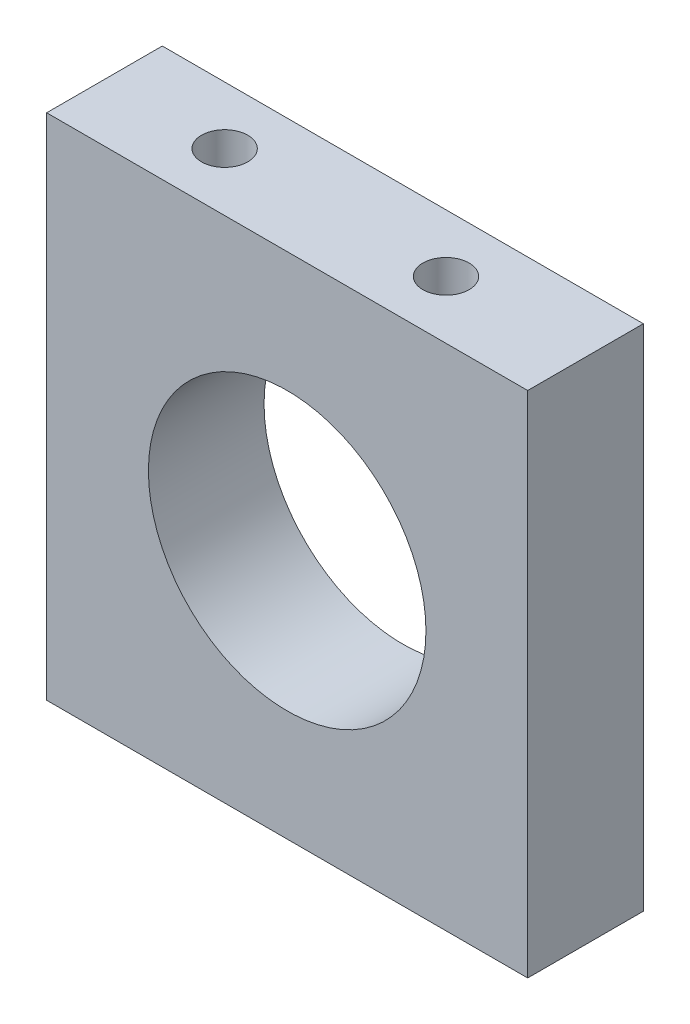
SolidWorks part; units mm, degrees
ref_plane "Front Plane" through (0, 0, 0) normal (0, 0, 1) x (1, 0, 0)
ref_plane "Top Plane" through (0, 0, 0) normal (0, 1, 0) x (1, 0, 0)
ref_plane "Right Plane" through (0, 0, 0) normal (1, 0, 0) x (0, 0, -1)
sketch "Sketch1" plane through (0, 0, 0) normal (0, 0, 1) x (1, 0, 0)
  line L0 (0, 76.2403) -> (0, -77.1776) construction
  line L1 (-114.2946, 0) -> (113.8013, 0) construction
  line L2 (-26, 0) -> (26, 0)
  line L3 (26, 0) -> (26, 55)
  line L4 (-26, 0) -> (-26, 55)
  line L5 (-26, 55) -> (26, 55)
  point P5 (0, 55)
  point P10 (0, 0)
  point P11 (0, 0)
  point P12 (0, 27.5)
  dimension "D1" = 26
  dimension "D2" = 55
  dimension "D3" = 27.5
extrude "Boss-Extrude1" add sketch "Sketch1" along normal blind 12.5
sketch "Sketch2" plane through (0, 0, 12.5) normal (0, 0, 1) x (1, 0, 0)
  line L0 (0, 63.268) -> (0, -9.268) construction
  line L1 (-26, 0) -> (26, 0) construction
  circle A0 centre (0, 27) radius 15
  point P3 (0, 27)
  dimension "D1" = 27
extrude "Cut-Extrude2" cut sketch "Sketch2" against normal through all
sketch "Sketch3" plane through (0, 55, 0) normal (0, 1, 0) x (1, 0, 0)
  circle A0 centre (-13.0309, -6.2292) radius 2.9819
  circle A1 centre (10.8978, -6.2292) radius 2.9791
  dimension "D1" = 5.9638
  dimension "D2" = 5.9581
hole_wizard "Ø5.0mm Dowel Hole1" positions "Sketch5" profile "Sketch6" hole size "Ø5.0" standard "ISO"
sketch "Sketch5" plane through (0, 55, 0) normal (0, 1, 0) x (1, 0, 0)
  point P0 (-13.0309, -6.2292)
  point P3 (10.8978, -6.2292)
sketch "Sketch6" plane through (-13.0309, 55, 6.2292) normal (1, 0, 0) x (0, 0, 1)
  line L0 (0, 0) -> (0, 11.5022)
  line L1 (0, 11.5022) -> (2.5, 10)
  line L2 (2.5, 10) -> (2.5, 0)
  line L5 (2.5, 0) -> (0, 0)
  line L10 (0, 11.5022) -> (-2.5, 10) construction
  line L11 (0, -6.35) -> (0, 107.95) construction
  dimension "Hole Dia." = 5
  dimension "Hole Depth" = 10
  dimension "Drill Angle" = 118
